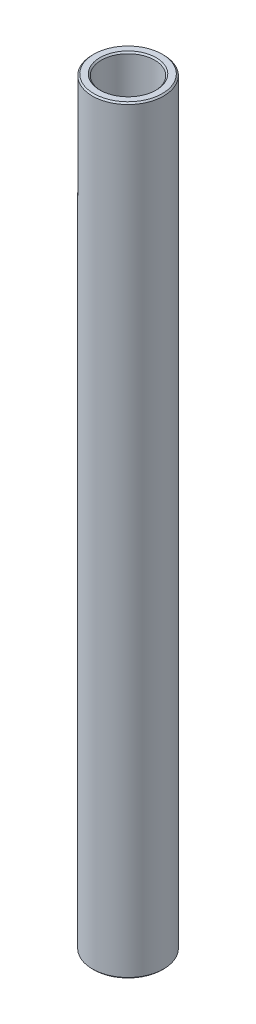
SolidWorks part; units mm, degrees
ref_plane "Front Plane" through (0, 0, 0) normal (0, 0, 1) x (1, 0, 0)
ref_plane "Top Plane" through (0, 0, 0) normal (0, 1, 0) x (1, 0, 0)
ref_plane "Right Plane" through (0, 0, 0) normal (1, 0, 0) x (0, 0, -1)
sketch "Sketch1" plane through (0, 0, 0) normal (0, 0, 1) x (1, 0, 0)
  line L0 (4.7625, 70.6437) -> (4.7625, 205.9781)
  line L1 (4.7625, 205.9781) -> (6.35, 205.9781)
  line L2 (6.35, 205.9781) -> (6.35, 70.6437)
  line L3 (6.35, 70.6437) -> (4.7625, 70.6437)
  line L4 (120.0875, 90.9128) -> (10.0875, 90.9128) construction
  line L6 (0, 61.1187) -> (0, 215.5031) construction
  dimension "D1" = 9.525
  dimension "D2" = 9.525
  dimension "D3" = 12.7
  dimension "D4" = 9.525
revolve "Revolve1" add sketch "Sketch1" angle 360 about L6
chamfer "Chamfer1" distance 0.254 angle 45 4 edges at (6.35, 205.9781, 0) (4.7625, 205.9781, 0) (4.7625, 70.6437, 0) (6.35, 70.6437, 0)
equation "\"D4@Sketch1\"=\"D1@Sketch1\""
